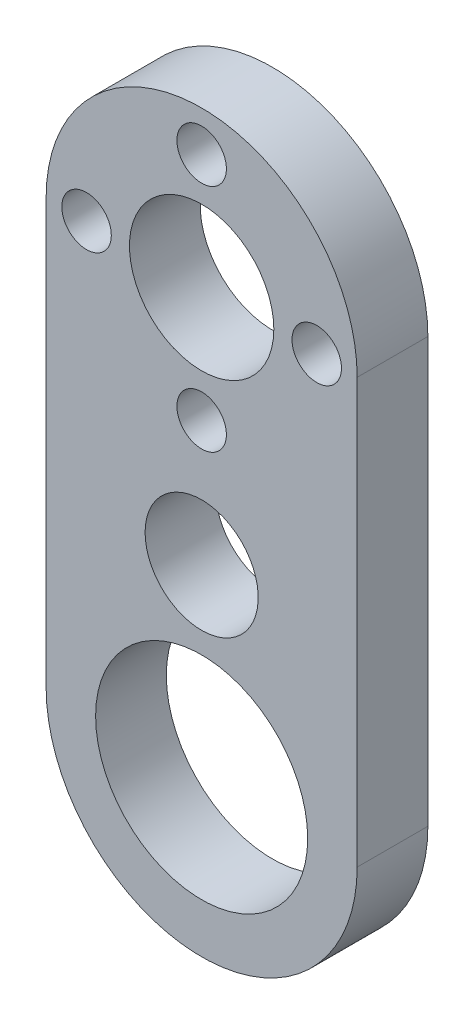
SolidWorks part; units mm, degrees
ref_plane "Plano frontal" through (0, 0, 0) normal (0, 0, 1) x (1, 0, 0)
ref_plane "Plano superior" through (0, 0, 0) normal (0, 1, 0) x (1, 0, 0)
ref_plane "Plano direito" through (0, 0, 0) normal (1, 0, 0) x (0, 0, -1)
sketch "Esboço1" plane through (0, 0, 0) normal (0, 0, 1) x (1, 0, 0)
  circle A0 centre (0, 0) radius 11
  circle A1 centre (0, 0) radius 5.105
  dimension "D1" = 22
  dimension "D2" = 10.21
extrude "Ressalto-extrusão1" add sketch "Esboço1" along normal blind 5
sketch "Esboço2" plane through (0, 0, 0) normal (0, 0, -1) x (-1, 0, 0)
  circle A0 centre (0, -8.14) radius 1.75
  circle A1 centre (0, 0) radius 5.105 construction
  dimension "D1" = 3.5
  dimension "D2" = 8.14
extrude "Corte-extrusão1" cut sketch "Esboço2" against normal blind 5
pattern_circular "PadrãoCircular1" count 4 over 360 about axis through (0, 0, 0) along (0, 0, 1) of "Corte-extrusão1"
sketch "Esboço3" plane through (0, 0, 0) normal (0, 0, -1) x (-1, 0, 0)
  line L0 (-11, 0) -> (-11, -30)
  line L1 (11, 0) -> (11, -30)
  circle A0 centre (0, 0) radius 11 construction
  arc A1 (11, -30) -> (-11, -30) centre (0, -30) cw
  circle A2 centre (0, -30) radius 7.5
  circle A3 centre (0, -17) radius 4
  circle A4 centre (0, 0) radius 5.105 construction
  arc A5 (-11, 0) -> (11, 0) centre (0, 0) ccw
  dimension "D1" = 15
  dimension "D3" = 8
  dimension "D4" = 17
  dimension "D2" = 30
extrude "Ressalto-extrusão2" add sketch "Esboço3" against normal blind 5
